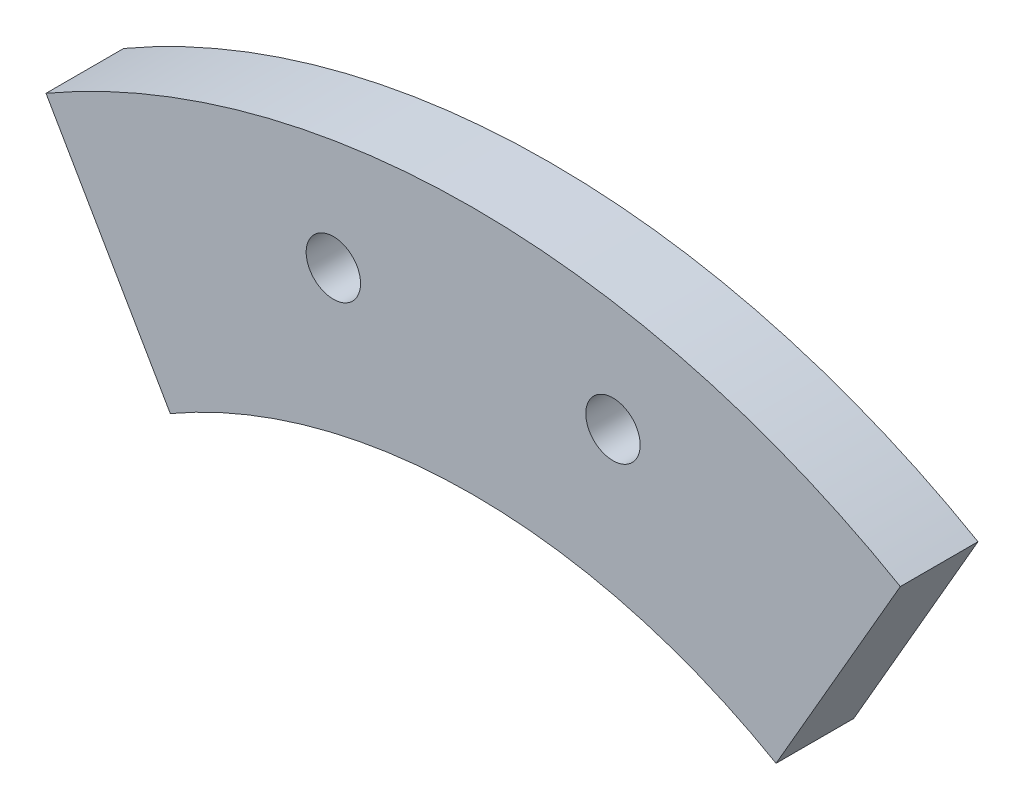
SolidWorks part; units mm, degrees
material "2024-T3"
ref_plane "Plan de face" through (0, 0, 0) normal (0, 0, 1) x (1, 0, 0)
ref_plane "Plan de dessus" through (0, 0, 0) normal (0, 1, 0) x (1, 0, 0)
ref_plane "Plan de droite" through (0, 0, 0) normal (1, 0, 0) x (0, 0, -1)
sketch "Esquisse2" plane through (0, 0, 0) normal (0, 0, 1) x (1, 0, 0)
  line L0 (0, 0) -> (0, 62.3433) construction
  line L1 (0, 0) -> (27.5, 47.6314)
  line L2 (0, 0) -> (-27.5, 47.6314)
  arc A0 (19.5, 33.775) -> (-19.5, 33.775) centre (0, 0) ccw
  arc A1 (27.5, 47.6314) -> (-27.5, 47.6314) centre (0, 0) ccw
  circle A2 centre (0, 0) radius 48 construction
  circle A3 centre (-9, 47.1487) radius 1.75
  circle A4 centre (9, 47.1487) radius 1.75
  dimension "D1" = 78
  dimension "D2" = 110
  dimension "D5" = 96
  dimension "D8" = 3.5
  dimension "D9" = 3.5
  dimension "D3" = 60
  dimension "D4" = 30
  dimension "D6" = 18
  dimension "D7" = 9
extrude "Boss.-Extru.1" add sketch "Esquisse2" along normal blind 5 contours A0 L0 A1 L2 | L0 A0 L1 A1
sketch "Esquisse3" plane through (0, 0, 0) normal (0, 0, -1) x (-1, 0, 0)
  circle A0 centre (0, 0) radius 39
  dimension "D1" = 78
extrude "Enlèv. mat.-Extru.1" cut sketch "Esquisse3" against normal through all
